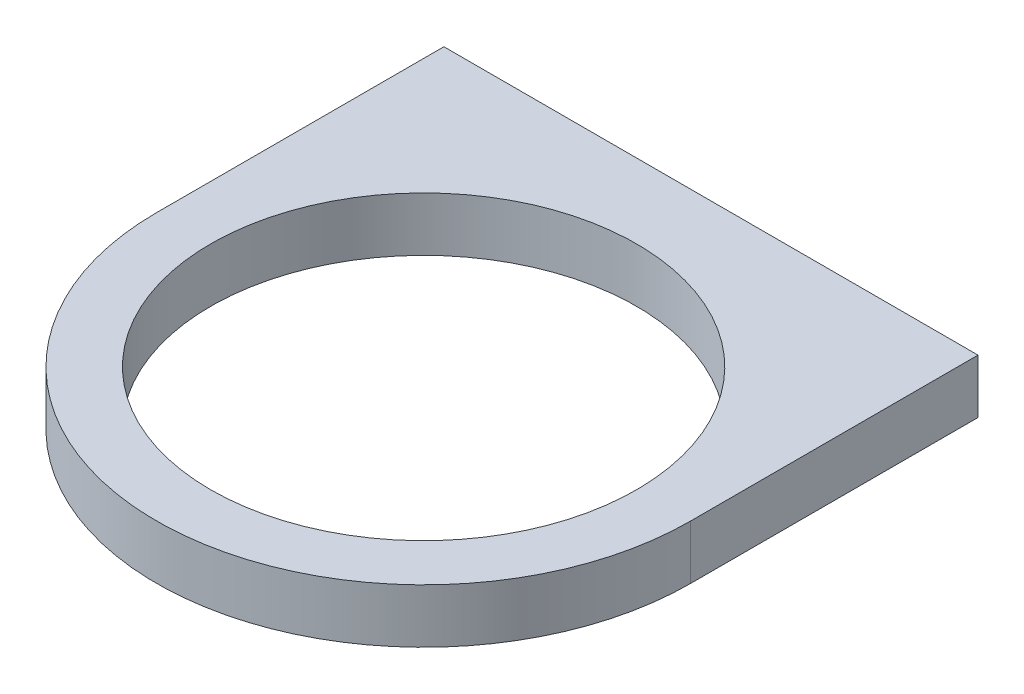
SolidWorks part; units mm, degrees
ref_plane "Front Plane" through (0, 0, 0) normal (0, 0, 1) x (1, 0, 0)
ref_plane "Top Plane" through (0, 0, 0) normal (0, 1, 0) x (1, 0, 0)
ref_plane "Right Plane" through (0, 0, 0) normal (1, 0, 0) x (0, 0, -1)
sketch "Sketch18" plane through (0, 0, 0) normal (0, 1, 0) x (1, 0, 0)
  line L0 (-39.5, 0) -> (-39.5, 42.5)
  line L1 (-39.5, 42.5) -> (39.5, 42.5)
  line L2 (39.5, 42.5) -> (39.5, 0)
  circle A0 centre (0, 0) radius 31.5
  arc A1 (-39.5, 0) -> (39.5, 0) centre (0, 0) ccw
  dimension "D1" = 63
  dimension "D2" = 8
  dimension "D3" = 42.5
extrude "Boss-Extrude13" add sketch "Sketch18" along normal blind 8
sketch "Sketch19" plane through (0, 0, 0) normal (0, -1, 0) x (1, 0, 0)
  line L0 (39.5, -42.5) -> (-39.5, -42.5) construction
  line L1 (-39.5, -42.5) -> (-39.5, 0) construction
  line L2 (39.5, 0) -> (39.5, -42.5) construction
  circle A0 centre (-35.5, -38.5) radius 2
  circle A1 centre (35.5, -38.5) radius 2
  dimension "D1" = 4
  dimension "D2" = 4
  dimension "D3" = 4
  dimension "D4" = 4
extrude "Boss-Extrude14" add sketch "Sketch19" along normal blind 2
